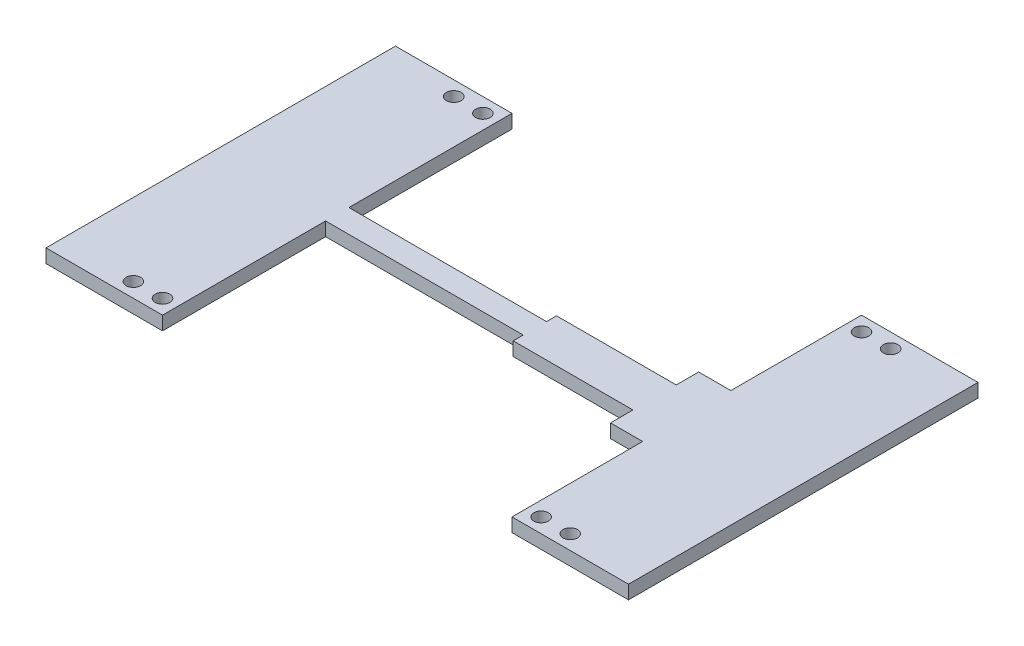
SolidWorks part; units mm, degrees
ref_plane "Front Plane" through (0, 0, 0) normal (0, 0, 1) x (1, 0, 0)
ref_plane "Top Plane" through (0, 0, 0) normal (0, 1, 0) x (1, 0, 0)
ref_plane "Right Plane" through (0, 0, 0) normal (1, 0, 0) x (0, 0, -1)
sketch "Sketch2" plane through (0, 0, 0) normal (0, 1, 0) x (1, 0, 0)
  line L5 (-63.5, 38.1) -> (63.5, 38.1)
  line L6 (-63.5, 38.1) -> (-63.5, -38.1)
  line L7 (-63.5, -38.1) -> (63.5, -38.1)
  line L12 (63.5, 38.1) -> (63.5, -38.1)
  line L13 (-63.5, 38.1) -> (63.5, -38.1) construction
  line L14 (-63.5, -38.1) -> (63.5, 38.1) construction
  point P0 (0, 0)
  point P19 (-4.4901, 29.8901)
  point P20 (-40.4112, -6.0309)
  point P21 (4.4901, -29.8901)
  point P22 (40.4112, 6.0309)
  dimension "D1" = 127
  dimension "D2" = 76.2
extrude "Boss-Extrude1" add sketch "Sketch2" along normal blind 2.9718
sketch "Sketch3" plane through (0, 2.9718, 0) normal (0, 1, 0) x (1, 0, 0)
  line L0 (4.9787, -2.54) -> (4.9787, -4.7248)
  line L13 (4.9787, -4.7248) -> (31.0867, -4.7248)
  line L22 (31.0867, -4.7248) -> (31.0867, -9.6141)
  line L27 (31.0867, -9.6141) -> (38.1, -9.6141)
  line L42 (38.1, -9.6141) -> (38.1, -27.94)
  line L51 (25.4, -38.1) -> (-25.4, -38.1)
  line L68 (-63.5, -38.1) -> (63.5, -38.1) construction
  line L69 (-38.1, -2.54) -> (4.9787, -2.54)
  line L70 (-38.1, -2.54) -> (-38.1, -27.94)
  line L74 (38.1, -27.94) -> (38.1, -38.1)
  line L75 (38.1, -38.1) -> (25.4, -38.1)
  line L77 (-38.1, -34.925) -> (-41.275, -34.925) construction
  line L79 (-38.1, -27.94) -> (-38.1, -38.1)
  line L80 (-38.1, -38.1) -> (-25.4, -38.1)
  line L82 (-41.275, -34.925) -> (-47.625, -34.925) construction
  line L83 (38.1, -34.925) -> (41.275, -34.925) construction
  line L84 (41.275, -34.925) -> (47.625, -34.925) construction
  circle A19 centre (41.275, -34.925) radius 1.5875
  circle A20 centre (47.625, -34.925) radius 1.5875
  circle A21 centre (-41.275, -34.925) radius 1.5875
  circle A22 centre (-47.625, -34.925) radius 1.5875
  point P1 (0, 0)
  point P19 (12.7, -34.925)
  point P20 (36.5125, -22.225)
  point P21 (12.7, -34.925)
  point P23 (39.6875, -22.225)
  dimension "D8" = 3.175
  dimension "D9" = 3.175
  dimension "D3" = 12.7
  dimension "D2" = 12.7
  dimension "D10" = 3.175
  dimension "D7" = 35.56
  dimension "D11" = 6.35
extrude "Cut-Extrude1" cut sketch "Sketch3" against normal blind 2.9718
mirror "Mirror1" about plane through (0, 0, 0) normal (0, 0, 1) of "Cut-Extrude1"
